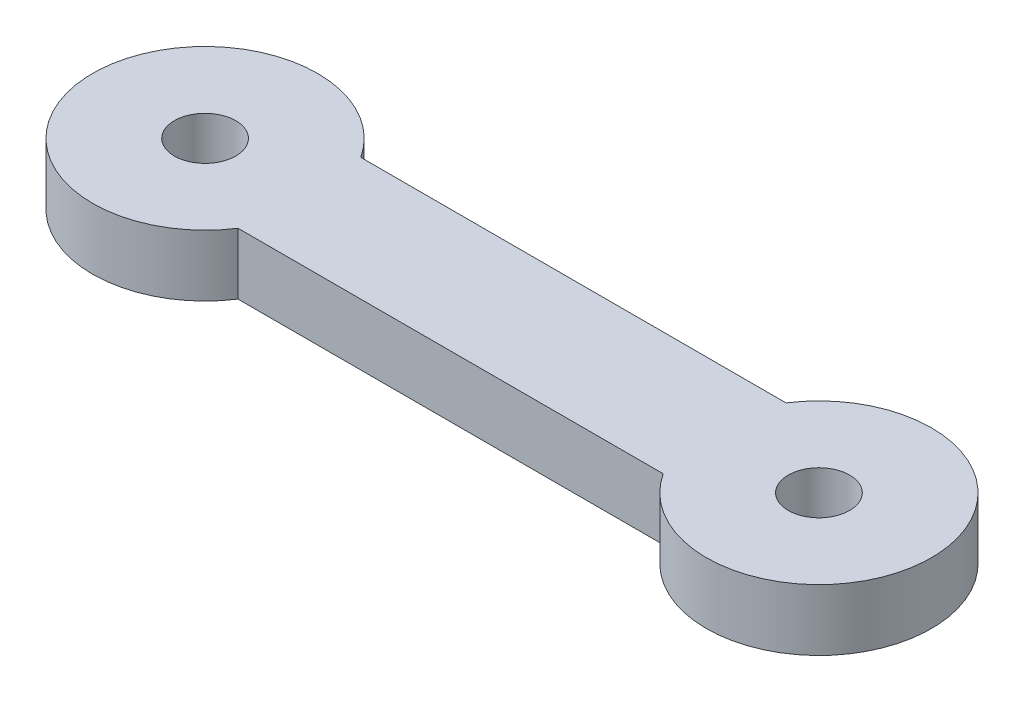
SolidWorks part; units mm, degrees
ref_plane "Front Plane" through (0, 0, 0) normal (0, 0, 1) x (1, 0, 0)
ref_plane "Top Plane" through (0, 0, 0) normal (0, 1, 0) x (1, 0, 0)
ref_plane "Right Plane" through (0, 0, 0) normal (1, 0, 0) x (0, 0, -1)
sketch "Sketch1" plane through (0, 0, 0) normal (0, 1, 0) x (1, 0, 0)
  line L0 (0, 0) -> (30, 0)
  line L1 (0, -3) -> (30, -3)
  line L2 (0, 3) -> (30, 3)
  circle A0 centre (0, 0) radius 1.5
  circle A1 centre (30, 0) radius 1.5
  circle A2 centre (0, 0) radius 5.5
  circle A3 centre (30, 0) radius 5.5
  dimension "D5" = 3
  dimension "D1" = 30
  dimension "D2" = 4
  dimension "D3" = 3
  dimension "D4" = 3
extrude "Boss-Extrude1" add sketch "Sketch1" along normal blind 3
